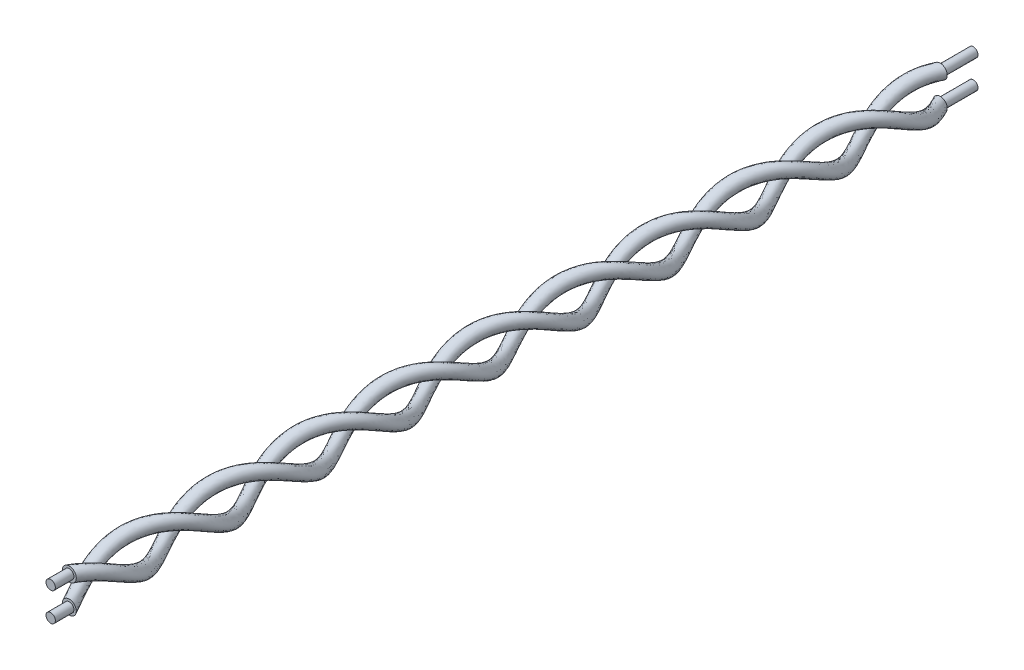
SolidWorks part; units mm, degrees
ref_plane "Front Plane" through (0, 0, 0) normal (0, 0, 1) x (1, 0, 0)
ref_plane "Top Plane" through (0, 0, 0) normal (0, 1, 0) x (1, 0, 0)
ref_plane "Right Plane" through (0, 0, 0) normal (1, 0, 0) x (0, 0, -1)
sketch "Sketch1" plane through (0, 0, 0) normal (0, 0, 1) x (1, 0, 0)
  circle A0 centre (0, 0) radius 1.5
  dimension "D1" = 3
curve "Helix/Spiral1" pitch 18.7 height 93.5 turns 5
sketch "Sketch2" plane through (0, 0, 0) normal (0, 0, 1) x (1, 0, 0)
  circle A0 centre (0, 0) radius 1.5
  dimension "D1" = 3
curve "Helix/Spiral2" pitch 18.7 height 93.5 turns 5
sketch "Sketch9" plane through (0, 0, 0) normal (0, 0, 1) x (1, 0, 0)
  circle A0 centre (0, 1.5235) radius 0.75
  circle A1 centre (0, -1.5534) radius 0.75
  dimension "D1" = 1.5
  dimension "D2" = 1.5
sweep "Sweep2" add profiles "Sketch9" path "Helix/Spiral1"
sketch "Sketch10" plane through (0, 0, 0) normal (0, 0, 1) x (1, 0, 0)
  circle A0 centre (0, 1.5235) radius 0.5
  circle A1 centre (0, -1.5534) radius 0.5
  dimension "D1" = 1
  dimension "D2" = 1
extrude "Boss-Extrude1" add sketch "Sketch10" along normal blind 2
sketch "Sketch11" plane through (0, 0, -93.5) normal (0, 0, -1) x (-1, 0, 0)
  circle A0 centre (0, 1.5235) radius 0.5
  circle A1 centre (0, -1.5534) radius 0.5
  dimension "D1" = 1
  dimension "D2" = 1
extrude "Boss-Extrude2" add sketch "Sketch11" along normal blind 3.5561
